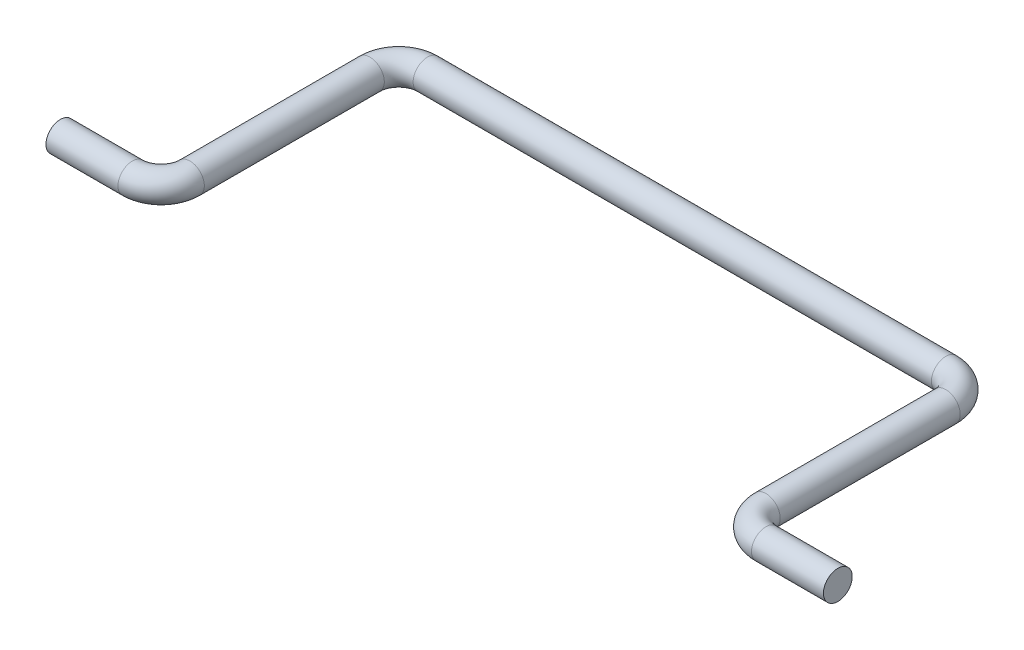
SolidWorks part; units mm, degrees
ref_plane "Front Plane" through (0, 0, 0) normal (0, 0, 1) x (1, 0, 0)
ref_plane "Top Plane" through (0, 0, 0) normal (0, 1, 0) x (1, 0, 0)
ref_plane "Right Plane" through (0, 0, 0) normal (1, 0, 0) x (0, 0, -1)
sketch "Sketch1" plane through (0, 0, 0) normal (0, 1, 0) x (1, 0, 0)
  line L0 (0, -150.3728) -> (0, 7368.2684) construction
  line L1 (-150.3728, 0) -> (7368.2684, 0) construction
  line L2 (-160.4113, 8.25) -> (7358.23, 8.25) construction
  line L3 (-13.5, -147.7382) -> (-13.5, 7370.9031) construction
  line L4 (13.5, -147.7382) -> (13.5, 7370.9031) construction
  line L5 (-10, -996.1346) -> (-10, 49003.8654) construction
  line L6 (10, -996.1346) -> (10, 49003.8654) construction
  line L7 (-13.5, 0) -> (-11, 0)
  line L8 (-10, 1) -> (-10, 7.25)
  line L9 (-9, 8.25) -> (9, 8.25)
  line L10 (10, 7.25) -> (10, 1)
  line L11 (11, 0) -> (13.5, 0)
  arc A0 (-10, 7.25) -> (-9, 8.25) centre (-9, 7.25) cw
  arc A1 (9, 8.25) -> (10, 7.25) centre (9, 7.25) cw
  arc A2 (10, 1) -> (11, 0) centre (11, 1) ccw
  arc A3 (-11, 0) -> (-10, 1) centre (-11, 1) ccw
  point P23 (-10, 8.25)
  point P26 (10, 8.25)
  point P29 (10, 0)
  point P32 (-10, 0)
  dimension "D4" = 1
  dimension "D1" = 8.25
  dimension "D2" = 13.5
  dimension "D3" = 10
ref_plane "Plane1" through (-13.5, 0, 0) normal (1, 0, 0) x (0, 0, -1)
sketch "Sketch4" plane through (-13.5, 0, 0) normal (1, 0, 0) x (0, 0, -1)
  circle A0 centre (0, 0) radius 0.5
sweep "Sweep1" add profiles "Sketch4" path "Sketch1"
